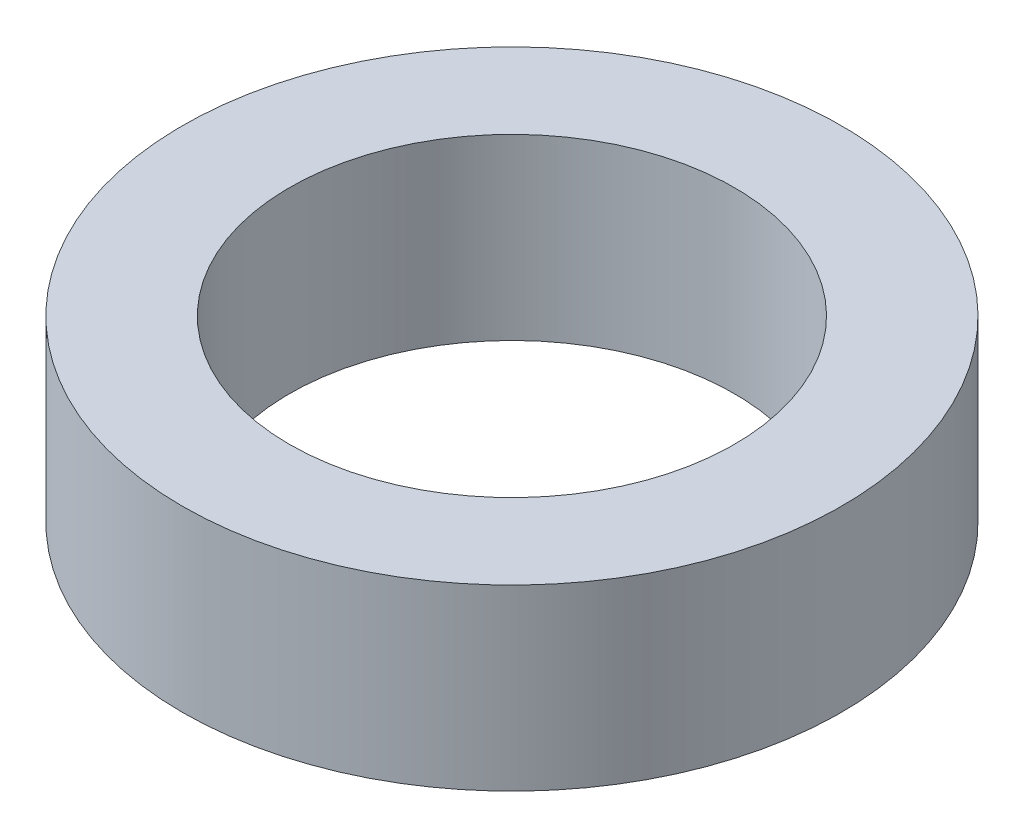
SolidWorks part; units mm, degrees
ref_plane "Front Plane" through (0, 0, 0) normal (0, 0, 1) x (1, 0, 0)
ref_plane "Top Plane" through (0, 0, 0) normal (0, 1, 0) x (1, 0, 0)
ref_plane "Right Plane" through (0, 0, 0) normal (1, 0, 0) x (0, 0, -1)
sketch "Sketch1" plane through (0, 0, 0) normal (0, 1, 0) x (1, 0, 0)
  circle A0 centre (0, 0) radius 4.05
  circle A1 centre (0, 0) radius 6
  dimension "D1" = 8.1
  dimension "D2" = 12
extrude "Boss-Extrude1" add sketch "Sketch1" along normal blind 3.25
